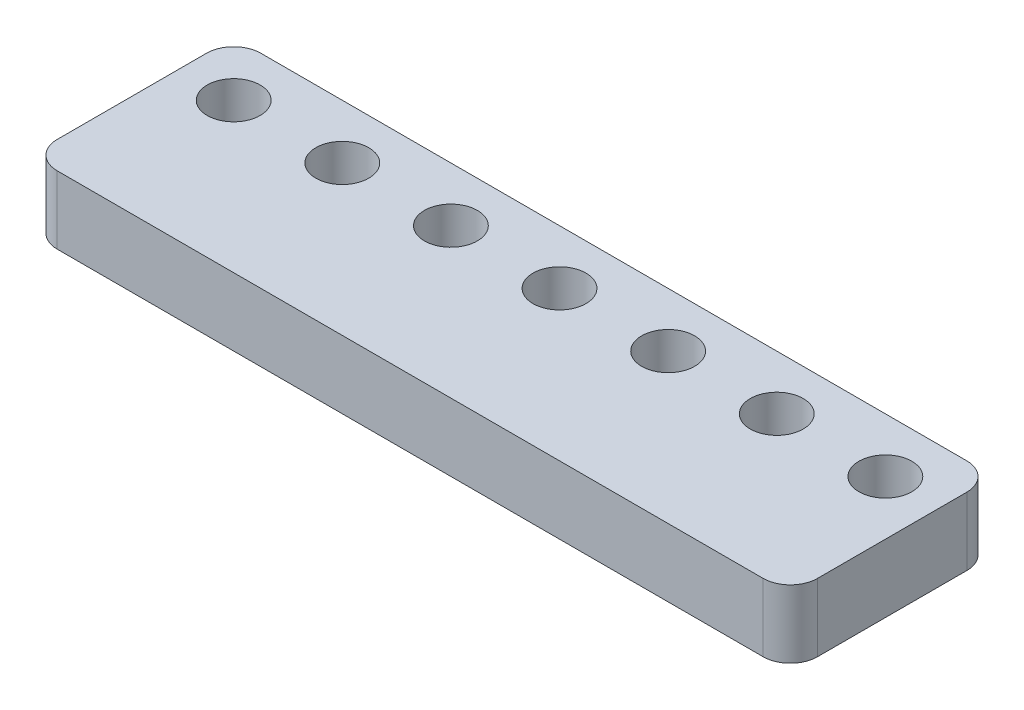
SolidWorks part; units mm, degrees
ref_plane "Front Plane" through (0, 0, 0) normal (0, 0, 1) x (1, 0, 0)
ref_plane "Top Plane" through (0, 0, 0) normal (0, 1, 0) x (1, 0, 0)
ref_plane "Right Plane" through (0, 0, 0) normal (1, 0, 0) x (0, 0, -1)
sketch "Sketch1" plane through (0, 0, 0) normal (0, 1, 0) x (1, 0, 0)
  line L1 (-54, 0) -> (-2, 0)
  line L2 (-56, -2) -> (-56, -13)
  line L3 (-54, -15) -> (-2, -15)
  line L4 (0, -2) -> (0, -13)
  arc A0 (-2, -15) -> (0, -13) centre (-2, -13) ccw
  arc A1 (-56, -13) -> (-54, -15) centre (-54, -13) ccw
  arc A2 (-54, 0) -> (-56, -2) centre (-54, -2) ccw
  arc A3 (-2, 0) -> (0, -2) centre (-2, -2) cw
  point P7 (0, -15)
  point P12 (-56, 0)
  point P15 (0, 0)
  dimension "D3" = 2
  dimension "D1" = 56
  dimension "D2" = 15
extrude "Boss-Extrude1" add sketch "Sketch1" along normal blind 5
sketch "Sketch2" plane through (0, 5, 0) normal (0, 1, 0) x (1, 0, 0)
  line L1 (0, -13) -> (0, -2) construction
  line L2 (-4, -4) -> (-56, -4) construction
  line L3 (-56, -2) -> (-56, -13) construction
  line L4 (-2, 0) -> (-54, 0) construction
  circle A0 centre (-4, -4) radius 1.95
  circle A1 centre (-12, -4) radius 1.95
  circle A2 centre (-76, -4) radius 1.95
  circle A3 centre (-68, -4) radius 1.95
  circle A4 centre (-60, -4) radius 1.95
  circle A5 centre (-52, -4) radius 1.95
  circle A6 centre (-44, -4) radius 1.95
  circle A7 centre (-36, -4) radius 1.95
  circle A8 centre (-28, -4) radius 1.95
  circle A9 centre (-20, -4) radius 1.95
  dimension "D1" = 3.9
  dimension "D4" = 3.9
  dimension "D7" = 3.9
  dimension "D8" = 3.9
  dimension "D9" = 3.9
  dimension "D10" = 3.9
  dimension "D11" = 3.9
  dimension "D12" = 3.9
  dimension "D13" = 3.9
  dimension "D14" = 3.9
  dimension "D3" = 4
  dimension "D5" = 8
  dimension "D15" = 8
  dimension "D16" = 8
  dimension "D17" = 8
  dimension "D18" = 8
  dimension "D19" = 8
  dimension "D20" = 8
  dimension "D21" = 8
  dimension "D22" = 4
extrude "Cut-Extrude1" cut sketch "Sketch2" against normal through all
